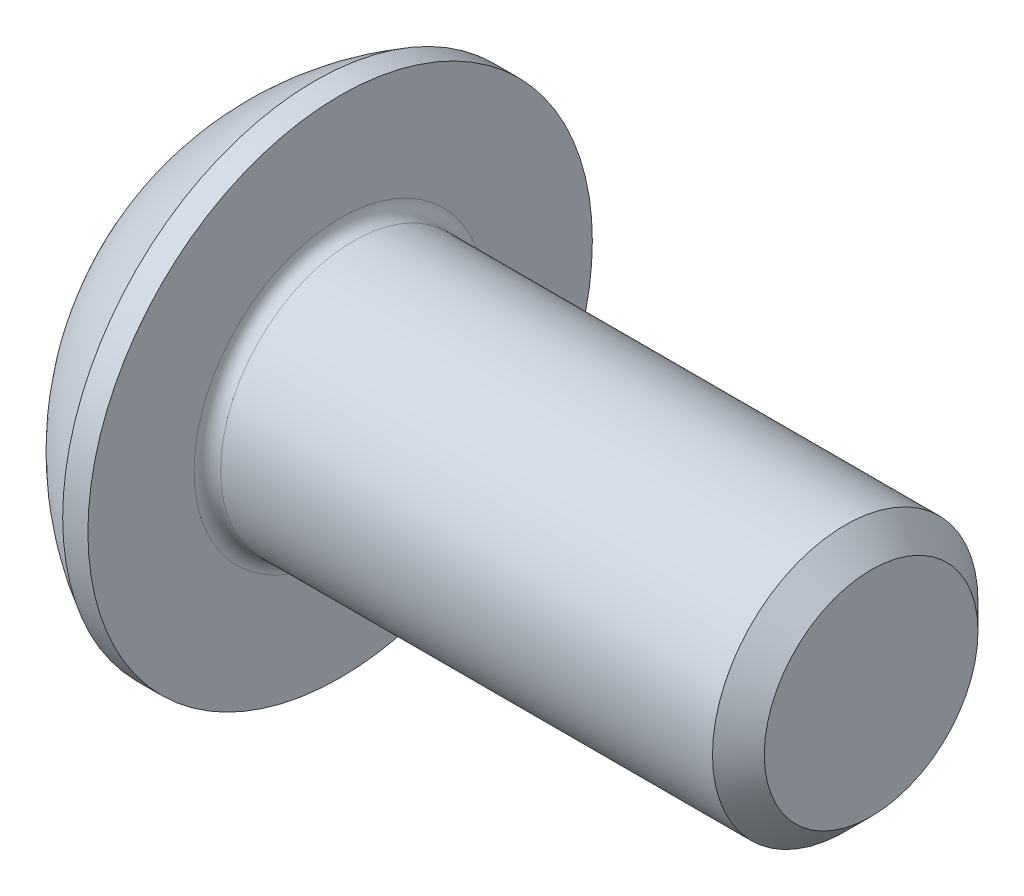
SolidWorks part; units mm, degrees
ref_plane "Plane1" through (0, 0, 0) normal (0, 0, 1) x (1, 0, 0)
ref_plane "Plane2" through (0, 0, 0) normal (0, 1, 0) x (1, 0, 0)
ref_plane "Plane3" through (0, 0, 0) normal (1, 0, 0) x (0, 0, -1)
other "Configuration Table"
sketch "BodySke" plane through (0, 0, 0) normal (0, 0, 1) x (1, 0, 0)
  line L0 (10.2, 0) -> (10.2, 1.61)
  line L1 (9.81, 2) -> (2.2, 2)
  line L2 (2.2, 2) -> (2.2, 3.8)
  line L3 (2.2, 3.8) -> (1.82, 3.8)
  line L4 (0, 0) -> (101.6, 0) construction
  line L5 (2.2, -3.8) -> (1.82, -3.8) construction
  line L6 (55.6768, -2) -> (2.2, -2) construction
  line L7 (10.2, 0) -> (0, 0)
  line L8 (0, 1.9) -> (0, -1.9) construction
  line L9 (0, 0) -> (0, 1.9)
  line L10 (10.2, 1.61) -> (9.81, 2)
  line L11 (10.2, -1.61) -> (9.81, -2) construction
  line L12 (2.9, 9.525) -> (2.9, -2) construction
  line L13 (2.2, 9.525) -> (2.2, -2) construction
  arc A1 (0, 1.9) -> (1.82, 3.8) centre (3.8853, 0) cw
  dimension "Head_side_ht" = 0.38
  dimension "Body_ch_ang" = 45
revolve "BaseBody" add sketch "BodySke" angle 360 about L4
cosmetic thread "ThreadCosmetic" [suppressed] parameters "Thread_length"=6.6, "Thread_minor"=3.22
fillet "Fillet1" radius 0.2 1 edges at (2.2, 0, 2)
sketch "Sketch2" plane through (0, 0, 0) normal (0, 0, 1) x (1, 0, 0)
  line L0 (0, 1.25) -> (1.3, 1.25)
  line L1 (1.3, 1.25) -> (2.0217, 0)
  line L3 (2.0217, 0) -> (0, 0)
  line L4 (0, 0) -> (0, 1.25)
  line L5 (0, -1.25) -> (1.3, -1.25) construction
  line L6 (0, 0) -> (47.625, 0) construction
  dimension "D2" = 60
  dimension "PreBroach_depth" = 1.3
  dimension "PreBroach_dia" = 2.5
revolve "PreBroach" cut sketch "Sketch2" angle 360 about L6
sketch "Sketch3" plane through (0, 0, 0) normal (1, 0, 0) x (0, 0, -1)
  line L0 (-1.25, -0.7217) -> (-1.25, 0.7217)
  line L1 (-1.25, 0.7217) -> (0, 1.4434)
  line L2 (0, 1.4434) -> (1.25, 0.7217)
  line L3 (1.25, 0.7217) -> (1.25, -0.7217)
  line L4 (1.25, -0.7217) -> (0, -1.4434)
  line L5 (0, -1.4434) -> (-1.25, -0.7217)
  dimension "Hex_size" = 2.5
  dimension "D3" = 2.5
  dimension "D1" = 1.25
  dimension "D2" = 1.25
extrude "Hex" cut sketch "Sketch3" along normal blind 1.3
sketch "ThdSchSke" plane through (0, 0, 0) normal (0, 0, 1) x (1, 0, 0)
  line L0 (3.6, -1.61) -> (3.3269, -2)
  line L1 (3.6, -1.61) -> (3.8731, -2)
  line L2 (3.8731, -2) -> (3.8731, -2.5)
  line L3 (-3.175, 0) -> (5.1513, 0) construction
  line L5 (3.8731, -2.5) -> (3.3269, -2.5)
  line L6 (3.3269, -2.5) -> (3.3269, -2)
  dimension "SideAngle" = 55
  dimension "VeeAngle" = 70
revolve "ThreadSchematic" [suppressed] cut sketch "ThdSchSke" angle 360 about L3
pattern_linear "ThdSchPat" [suppressed]
equation "\"D1@BodySke\" = \"Head_dia@BodySke\" * .5"
equation "\"Thread_minor@ThreadCosmetic\" = \"Minor_dia@BodySke\""
equation "\"D1@Sketch3\" = \"Hex_size@Sketch3\" / 2"
equation "\"D2@Sketch3\" = \"D1@Sketch3\""
equation "\"D3@Sketch3\" = \"Hex_size@Sketch3\""
equation "\"Thread_length@ThreadCosmetic\" = ((sgn( (\"Length@BodySke\" - \"Advance@BodySke\" * 2.0) - \"Thread_nom@BodySke\" )-1)*( (\"Length@BodySke\" - \"Advance@BodySke\" * 2.0) - \"Thread_nom@BodySke\" ))/-2+ \"Thread_nom@BodySke\""
equation "\"Thread_minor@ThdSchSke\" = \"Minor_dia@BodySke\""
equation "\"Diameter@ThdSchSke\" = \"Diameter@BodySke\""
equation "\"Overcut@ThdSchSke\" = \"Diameter@BodySke\" * 1.25"
equation "\"Start@ThdSchSke\" = \"Head_ht@BodySke\" + \"Length@BodySke\" - \"Thread_length@ThreadCosmetic\"  '---Non-countersunk---"
equation "\"Num_threads@ThdSchPat\" = int( \"Thread_length@ThreadCosmetic\" / \"Advance@BodySke\" + 0.999 )  + 1"
equation "\"Advance@ThdSchPat\" = \"Thread_length@ThreadCosmetic\" /  (\"Num_threads@ThdSchPat\" - 1) 'relax it"
equation "\"Num_threads@ThdSchPat\" = \"Num_threads@ThdSchPat\" - sgn( \"Num_threads@ThdSchPat\" - 1) '---chamfered tips only---"
